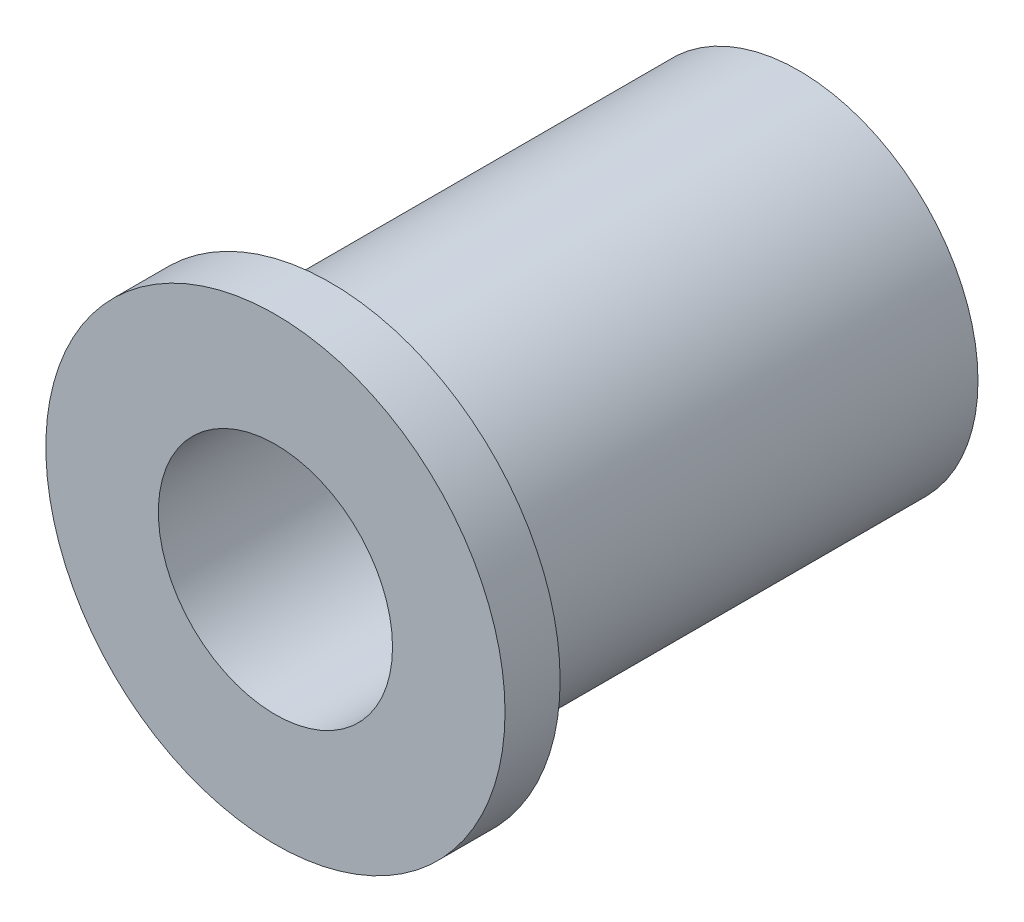
SolidWorks part; units mm, degrees
ref_plane "Front Plane" through (0, 0, 0) normal (0, 0, 1) x (1, 0, 0)
ref_plane "Top Plane" through (0, 0, 0) normal (0, 1, 0) x (1, 0, 0)
ref_plane "Right Plane" through (0, 0, 0) normal (1, 0, 0) x (0, 0, -1)
sketch "Sketch1" plane through (0, 0, 0) normal (0, 0, 1) x (1, 0, 0)
  circle A0 centre (0, 0) radius 4.953
  circle A1 centre (0, 0) radius 3.2385
  dimension "D1" = 9.906
  dimension "D2" = 6.477
extrude "Boss-Extrude1" add sketch "Sketch1" along normal blind 14.478
sketch "Sketch2" plane through (0, 0, 14.478) normal (0, 0, 1) x (1, 0, 0)
  circle A0 centre (0, 0) radius 3.2385
  circle A1 centre (0, 0) radius 6.35
  dimension "D1" = 12.7
extrude "Boss-Extrude2" add sketch "Sketch2" against normal blind 1.524
